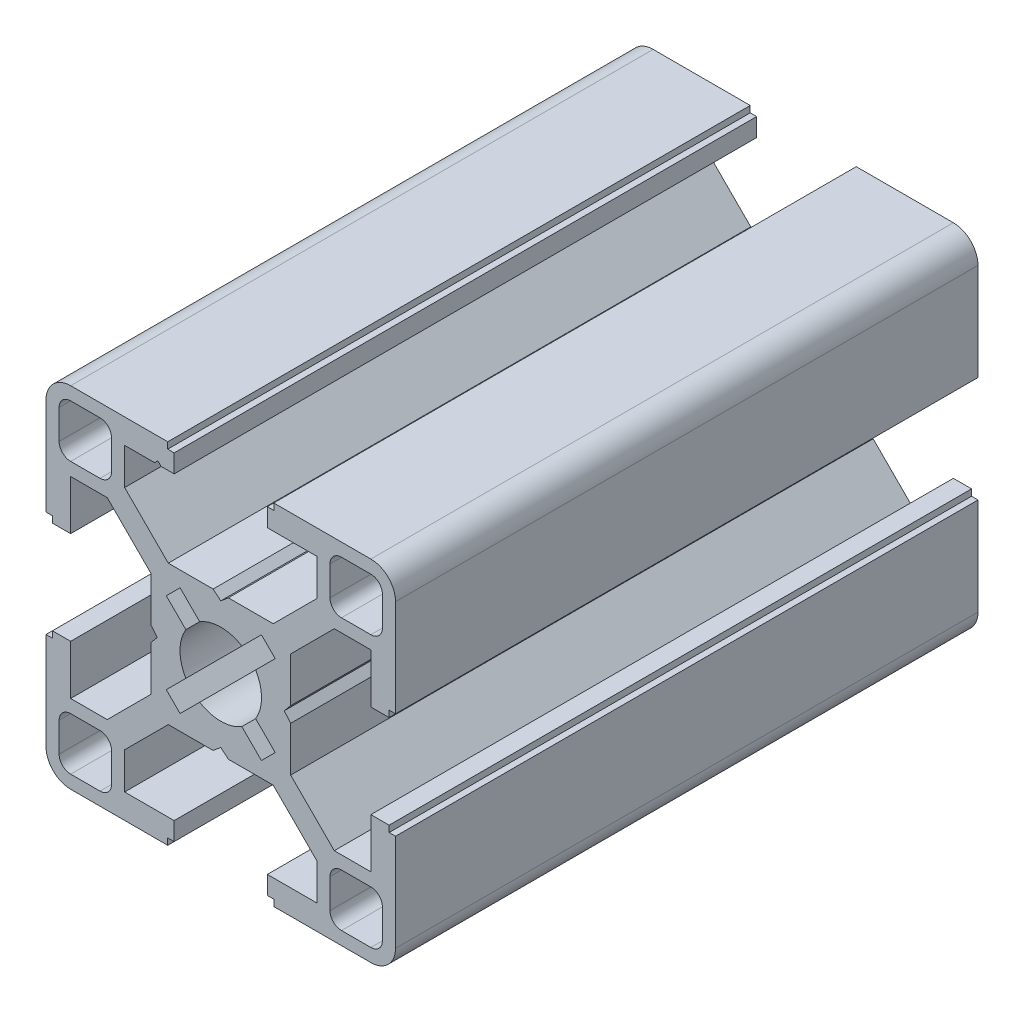
SolidWorks part; units mm, degrees
material "6061-T6 (SS)"
ref_plane "Front Plane" through (0, 0, 0) normal (0, 0, 1) x (1, 0, 0)
ref_plane "Top Plane" through (0, 0, 0) normal (0, 1, 0) x (1, 0, 0)
ref_plane "Right Plane" through (0, 0, 0) normal (1, 0, 0) x (0, 0, -1)
sketch "Sketch2" plane through (0, 0, 0) normal (0, 0, 1) x (1, 0, 0)
  line L0 (0, 15) -> (0, -15) construction
  line L1 (-15, 0) -> (15, 0) construction
  line L2 (4, -15) -> (15, -15)
  line L3 (15, -15) -> (15, -4)
  line L4 (4, -15) -> (4, -12.885)
  line L6 (8.25, -9.7455) -> (4.5045, -6)
  line L7 (0, 0) -> (15, -15) construction
  line L8 (15, -4) -> (12.885, -4)
  line L11 (4.55, -15) -> (4.55, -14.45) construction
  line L12 (4, -12.885) -> (8.25, -12.885)
  line L13 (8.25, -12.885) -> (8.25, -9.7455)
  line L14 (4.55, -14.45) -> (4, -14.45) construction
  line L15 (14.45, -4) -> (14.45, -4.55) construction
  line L16 (14.45, -4.55) -> (15, -4.55) construction
  line L17 (12.885, -4) -> (12.885, -8.25)
  line L18 (12.885, -8.25) -> (9.7455, -8.25)
  line L19 (9.7455, -8.25) -> (6, -4.5045)
  line L20 (7.8728, -6.3772) -> (6.3772, -7.8728) construction
  line L21 (11.625, -13.875) -> (11.625, -15) construction
  line L22 (9.375, -13.875) -> (13.875, -13.875)
  line L23 (9.375, -13.875) -> (9.375, -9.375)
  line L24 (9.375, -9.375) -> (13.875, -9.375)
  line L25 (13.875, -13.875) -> (13.875, -9.375)
  line L26 (11.625, -9.375) -> (11.625, -13.875) construction
  line L27 (9.375, -11.625) -> (13.875, -11.625) construction
  line L28 (13.875, -11.625) -> (15, -11.625) construction
  line L29 (8.25, -12.885) -> (9.375, -12.885) construction
  line L30 (4.5045, -6) -> (0.6555, -6)
  line L31 (0.6555, -6) -> (0, -5.45)
  line L32 (0, -6) -> (0, -5.45) construction
  circle A0 centre (0, 0) radius 3.5
  arc A2 (9.375, -12.885) -> (10.365, -13.875) centre (10.365, -12.885) ccw construction
  point P8 (0, -6)
  point P15 (4.55, -15)
  point P16 (7.125, -7.125)
  point P33 (11.625, -11.625)
  dimension "Center Hole Diameter" = 7
  dimension "Rail Height" = 30
  dimension "Rail Width" = 30
  dimension "T-Slot Width" = 8
  dimension "Slot Depth" = 9
  dimension "Slot Inner Width" = 16.5
  dimension "Step Width" = 9.1
  dimension "D1" = 1.125
  dimension "D2" = 2.115
  dimension "D3" = 50
sketch "Sketch3" plane through (0, 0, 0) normal (1, 0, 0) x (0, 0, -1)
  line L0 (-76.2, -15) -> (76.2, -15) construction
  line L1 (-50.8, 0) -> (50.8, 0) construction
  point P6 (-50.8, 0)
  point P8 (50.8, 0)
  dimension "Length" = 152.4
  dimension "D1" = 25.4
sketch "Sketch4" plane through (0, 0, 0) normal (0, 0, 1) x (1, 0, 0)
  line L22 (0, -5.45) -> (0.6555, -6)
  line L23 (0.6555, -6) -> (4.5045, -6)
  line L24 (4.5045, -6) -> (8.25, -9.7455)
  line L25 (8.25, -9.7455) -> (8.25, -12.885)
  line L26 (8.25, -12.885) -> (4, -12.885)
  line L27 (4, -12.885) -> (4, -14.45)
  line L28 (4, -14.45) -> (4.55, -14.45)
  line L29 (4.55, -14.45) -> (4.55, -15)
  line L30 (4.55, -15) -> (12.885, -15)
  line L31 (4, -15) -> (15, -15) construction
  line L32 (15, -15) -> (15, -4) construction
  line L33 (15, -12.885) -> (15, -4.55)
  line L34 (15, -4.55) -> (14.45, -4.55)
  line L35 (14.45, -4.55) -> (14.45, -4)
  line L36 (14.45, -4) -> (12.885, -4)
  line L37 (12.885, -4) -> (12.885, -8.25)
  line L38 (12.885, -8.25) -> (9.7455, -8.25)
  line L39 (9.7455, -8.25) -> (6, -4.5045)
  line L40 (6, -4.5045) -> (6, -0.6555)
  line L41 (6, -0.6555) -> (5.45, 0)
  line L42 (-15, 0) -> (15, 0) construction
  line L43 (0, -5.45) -> (0, -3.5)
  line L44 (0, 15) -> (0, -15) construction
  line L45 (3.5, 0) -> (5.45, 0)
  line L46 (1.8108, -2.9952) -> (3.4913, -4.6757)
  line L47 (3.4913, -4.6757) -> (4.6757, -3.4913)
  line L48 (4.6757, -3.4913) -> (2.9952, -1.8108)
  line L49 (0, 0) -> (15, -15) construction
  line L50 (9.375, -13.875) -> (13.875, -13.875) construction
  line L51 (13.875, -13.875) -> (13.875, -9.375) construction
  line L52 (9.375, -13.875) -> (9.375, -9.375) construction
  line L53 (9.375, -9.375) -> (13.875, -9.375) construction
  line L54 (9.375, -10.365) -> (9.375, -12.885)
  line L55 (10.365, -13.875) -> (12.885, -13.875)
  line L56 (13.875, -12.885) -> (13.875, -10.365)
  line L57 (10.365, -9.375) -> (12.885, -9.375)
  arc A12 (12.885, -15) -> (15, -12.885) centre (12.885, -12.885) ccw
  circle A13 centre (0, 0) radius 3.5 construction
  arc A14 (0, -3.5) -> (1.8108, -2.9952) centre (0, 0) ccw
  arc A15 (3.5, 0) -> (2.9952, -1.8108) centre (0, 0) cw
  circle A16 centre (0, 0) radius 5.775 construction
  arc A17 (9.375, -12.885) -> (10.365, -13.875) centre (10.365, -12.885) ccw
  arc A18 (9.375, -12.885) -> (10.365, -13.875) centre (10.365, -12.885) ccw construction
  arc A19 (12.885, -13.875) -> (13.875, -12.885) centre (12.885, -12.885) ccw
  arc A20 (9.375, -10.365) -> (10.365, -9.375) centre (10.365, -10.365) cw
  arc A21 (12.885, -9.375) -> (13.875, -10.365) centre (12.885, -10.365) cw
  point P40 (4.0835, -4.0835)
  dimension "D1" = 11.55
  dimension "D2" = 0.22
extrude "Boss-Extrude1" add sketch "Sketch4" along normal mid plane 50
mirror "Mirror1" about plane through (0, 0, 0) normal (1, 0, 0) of bodies 134
mirror "Mirror2" about plane through (0, 0, 0) normal (0, 1, 0) of bodies 135
sketch "Sketch5" plane through (0, 0, 25) normal (0, 0, 1) x (1, 0, 0)
  line L0 (-5.675, 12.885) -> (-5.4, 13.16)
  line L1 (-8.25, 12.885) -> (-4, 12.885) construction
  line L2 (-5.4, 13.16) -> (-5.125, 12.885)
  line L3 (0, 15) -> (0, -15) construction
  line L4 (-5.675, 12.885) -> (-5.125, 12.885)
  dimension "D1" = 0.275
  dimension "D2" = 5.4
extrude "Cut-Extrude1" cut sketch "Sketch5" against normal through all both and the other way through all
sketch "Sketch6" plane through (0, 0, 25) normal (0, 0, 1) x (1, 0, 0)
  line L0 (-15, 4.55) -> (-15, -4.55) construction
  line L1 (15, 4.55) -> (15, -4.55) construction
  line L2 (-4.55, 15) -> (4.55, 15) construction
  line L3 (4.55, -15) -> (-4.55, -15) construction
  point P16 (0, 15)
  point P17 (15, 0)
  point P18 (0, -15)
  point P19 (-15, 0)
equation "\"D1@Boss-Extrude1\"=\"Length@Sketch3\""
equation "\"D1@Sketch2\"=\"Slot Depth@Sketch2\"*0.125"
equation "\"D2@Sketch2\"=\"Slot Depth@Sketch2\"*0.235"
equation "\"D1@Sketch4\"=\"Center Hole Diameter@Sketch2\"*1.65"
equation "\"D2@Sketch4\"=(\"Step Width@Sketch2\"-\"T-Slot Width@Sketch2\")*0.2"
equation "\"D1@Sketch5\"=(\"Step Width@Sketch2\"-\"T-Slot Width@Sketch2\")*0.5*0.5"
equation "\"D2@Sketch5\"=\"T-Slot Width@Sketch2\"*1.35*0.5"
